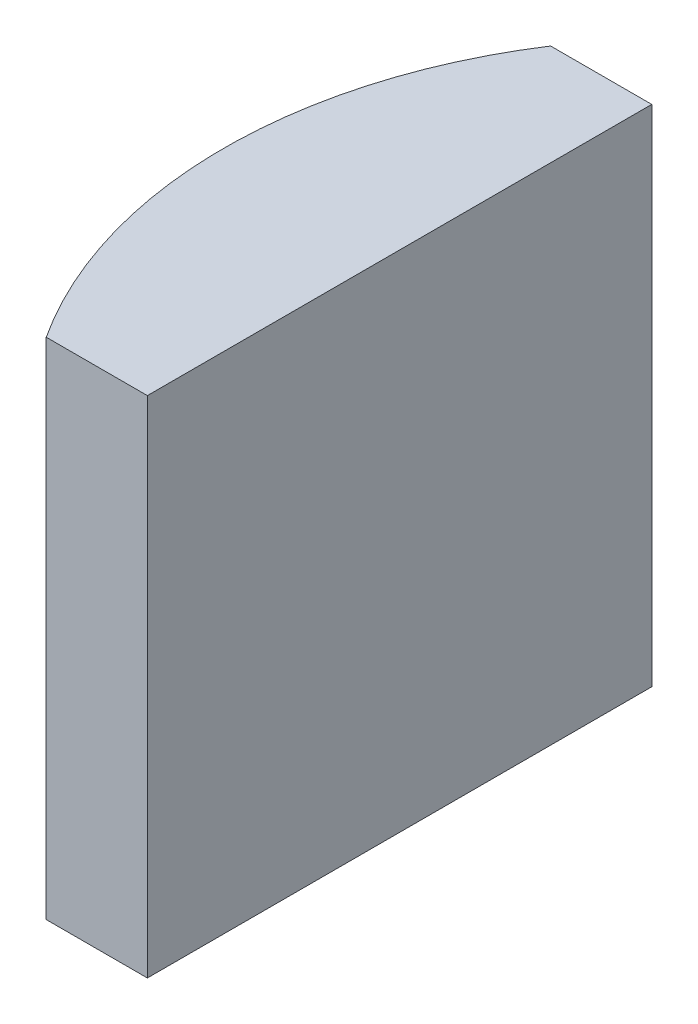
SolidWorks part; units mm, degrees
ref_plane "前视基准面" through (0, 0, 0) normal (0, 0, 1) x (1, 0, 0)
ref_plane "上视基准面" through (0, 0, 0) normal (0, 1, 0) x (1, 0, 0)
ref_plane "右视基准面" through (0, 0, 0) normal (1, 0, 0) x (0, 0, -1)
sketch "草图1" plane through (0, 0, 0) normal (0, 1, 0) x (1, 0, 0)
  line L0 (-4.6849, 0) -> (10.8051, 0) construction
  line L1 (-3.3198, 5) -> (-1.3148, 5)
  line L2 (-3.3198, -5) -> (-1.3148, -5)
  line L3 (-1.3148, 5) -> (-1.3148, -5)
  arc A0 (-3.3198, 5) -> (-3.3198, -5) centre (4.3552, 0) ccw
  point P2 (-4.8048, 0)
  point P4 (-1.3148, 0)
  dimension "D2" = 5
  dimension "D3" = 9.16
  dimension "D4" = 3.49
  dimension "D1" = 5
extrude "凸台-拉伸1" add sketch "草图1" along normal blind 10
